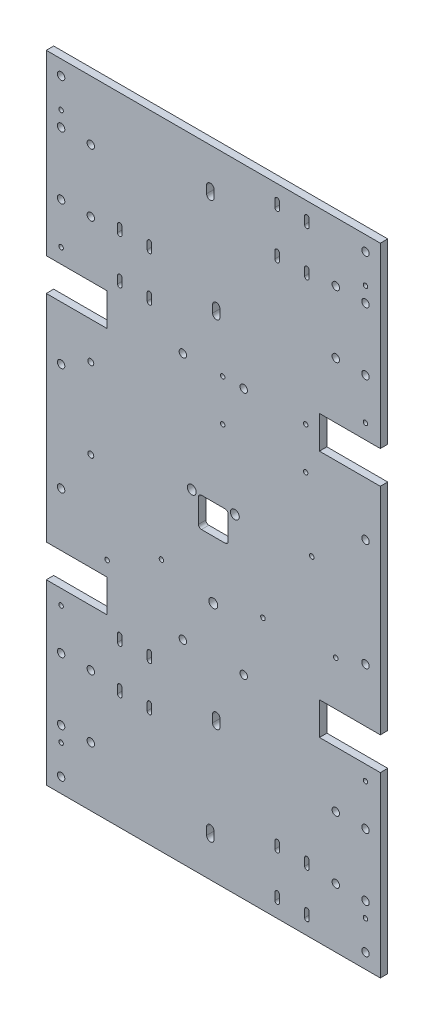
SolidWorks part; units mm, degrees
ref_plane "Front Plane" through (0, 0, 0) normal (0, 0, 1) x (1, 0, 0)
ref_plane "Top Plane" through (0, 0, 0) normal (0, 1, 0) x (1, 0, 0)
ref_plane "Right Plane" through (0, 0, 0) normal (1, 0, 0) x (0, 0, -1)
sketch "Sketch1" plane through (0, 0, 0) normal (0, 0, 1) x (1, 0, 0)
  line L0 (-112.5, 72.5) -> (-112.5, -72.5)
  line L2 (-112.5, 244.5) -> (-112.5, 94.5)
  line L4 (112.5, 244.5) -> (112.5, 94.5)
  line L5 (-112.5, 244.5) -> (112.5, -244.5) construction
  line L6 (-112.5, -244.5) -> (112.5, 244.5) construction
  line L7 (-112.5, 94.5) -> (-71.5, 94.5)
  line L10 (-71.5, 94.5) -> (-71.5, 72.5)
  line L11 (112.5, 94.5) -> (71.5, 94.5)
  line L13 (112.5, 72.5) -> (71.5, 72.5)
  line L14 (71.5, 94.5) -> (71.5, 72.5)
  line L15 (-112.5, -94.5) -> (-71.5, -94.5)
  line L17 (-112.5, -72.5) -> (-71.5, -72.5)
  line L18 (-71.5, -94.5) -> (-71.5, -72.5)
  line L19 (112.5, -72.5) -> (71.5, -72.5)
  line L21 (112.5, -94.5) -> (71.5, -94.5)
  line L22 (71.5, -72.5) -> (71.5, -94.5)
  line L23 (112.5, 72.5) -> (112.5, -72.5)
  line L24 (112.5, -94.5) -> (112.5, -244.5)
  line L25 (-112.5, -94.5) -> (-112.5, -244.5)
  line L28 (-112.5, 72.5) -> (-71.5, 72.5)
  line L30 (-112.5, -244.5) -> (112.5, -244.5) construction
  line L31 (112.5, -244.5) -> (-112.5, -244.5)
  line L32 (112.5, 244.5) -> (-112.5, 244.5)
  point P0 (0, 0)
  dimension "D2" = 225
  dimension "D3" = 41
  dimension "D6" = 22
  dimension "D7" = 22
  dimension "D8" = 41
  dimension "D9" = 41
  dimension "D10" = 22
  dimension "D12" = 145
  dimension "D67" = 150
extrude "Boss-Extrude1" add sketch "Sketch1" along normal blind 5
sketch "Sketch4" plane through (0, 0, 5) normal (0, 0, 1) x (1, 0, 0)
  line L0 (-112.5, 244.5) -> (-112.5, 94.5) construction
  line L1 (-112.5, 94.5) -> (-71.5, 94.5) construction
  circle A0 centre (-102.5, 174.31) radius 2.5
  circle A1 centre (-102.5, 132.31) radius 2.5
  circle A6 centre (-82.5, 174.31) radius 2.5
  circle A7 centre (-82.5, 132.31) radius 2.5
  dimension "D9" = 5
  dimension "D10" = 10
  dimension "D11" = 37.81
  dimension "D12" = 42
  dimension "D13" = 10
  dimension "D2" = 42
  dimension "D3" = 20
  dimension "D4" = 20
  dimension "D5" = 37.81
extrude "Cut-Extrude2" cut sketch "Sketch4" against normal blind 10
mirror "Mirror1" about plane through (0, 0, 0) normal (1, 0, 0) of "Cut-Extrude2"
mirror "Mirror2" about plane through (0, 0, 0) normal (0, 1, 0) of "Mirror1", "Cut-Extrude2"
sketch "Sketch5" plane through (0, 0, 5) normal (0, 0, 1) x (1, 0, 0)
  line L0 (-112.5, 244.5) -> (-112.5, 94.5) construction
  line L1 (-71.5, 72.5) -> (-112.5, 72.5) construction
  line L2 (-112.5, 72.5) -> (-112.5, -72.5) construction
  line L3 (-112.5, -72.5) -> (-71.5, -72.5) construction
  line L4 (-112.5, -94.5) -> (-112.5, -244.5) construction
  line L5 (112.5, -72.5) -> (112.5, 72.5) construction
  line L6 (112.5, 72.5) -> (71.5, 72.5) construction
  line L7 (-71.5, -72.5) -> (-71.5, -94.5) construction
  line L8 (71.5, -94.5) -> (71.5, -72.5) construction
  line L9 (-71.5, -83.5) -> (71.5, -83.5) construction
  line L10 (-71.5, 83.5) -> (71.5, 83.5) construction
  line L11 (-71.5, 94.5) -> (-71.5, 72.5) construction
  line L12 (71.5, 72.5) -> (71.5, 94.5) construction
  line L13 (112.5, 94.5) -> (112.5, 244.5) construction
  line L16 (0, 0) -> (82.5, 0) construction
  line L17 (71.5, -72.5) -> (112.5, -72.5) construction
  line L18 (0, 0) -> (0, -51.9509) construction
  line L28 (62.2018, 55.56) -> (62.2018, 83.5) construction
  line L29 (6.3218, 83.5) -> (6.3218, 55.56) construction
  line L30 (6.3218, 55.56) -> (62.2018, 55.56) construction
  line L31 (6.3218, 83.5) -> (62.2018, 55.56) construction
  line L32 (62.2018, 83.5) -> (6.3218, 83.5) construction
  circle A0 centre (-102.5, 204.31) radius 2.5
  circle A1 centre (-102.5, 174.31) radius 2.5 construction
  circle A2 centre (-102.5, 36.25) radius 2.5
  circle A3 centre (-102.5, -36.25) radius 2.5
  circle A5 centre (-102.5, -204.31) radius 2.5
  circle A6 centre (-102.5, -174.31) radius 2.5 construction
  circle A7 centre (102.5, -204.31) radius 2.5
  circle A8 centre (102.5, 204.31) radius 2.5
  circle A9 centre (102.5, 36.25) radius 2.5
  circle A11 centre (-20.5, -83.5) radius 2.5
  circle A12 centre (20.5, -83.5) radius 2.5
  circle A14 centre (-20.5, 83.5) radius 2.5
  circle A15 centre (20.5, 83.5) radius 2.5
  circle A16 centre (102.5, -174.31) radius 2.5 construction
  circle A17 centre (102.5, 174.31) radius 2.5 construction
  circle A19 centre (102.5, -36.25) radius 2.5
  circle A43 centre (62.2018, 83.5) radius 1.5
  circle A44 centre (62.2018, 55.56) radius 1.5
  circle A45 centre (6.3218, 55.56) radius 1.5
  circle A46 centre (6.3218, 83.5) radius 1.5
  dimension "D1" = 5
  dimension "D2" = 10
  dimension "D3" = 30
  dimension "D4" = 36.25
  dimension "D5" = 36.25
  dimension "D6" = 10
  dimension "D7" = 10
  dimension "D8" = 36.25
  dimension "D9" = 10
  dimension "D10" = 0
  dimension "D14" = 10
  dimension "D15" = 30
  dimension "D17" = 30
  dimension "D18" = 10
  dimension "D20" = 10
  dimension "D21" = 36.25
  dimension "D23" = 51
  dimension "D24" = 51
  dimension "D25" = 10
  dimension "D26" = 5
  dimension "D27" = 5
  dimension "D28" = 30
  dimension "D30" = 5
  dimension "D32" = 51
  dimension "D33" = 5
  dimension "D42" = 3
  dimension "D31" = 51
  dimension "D43" = 55.88
  dimension "D44" = 27.94
  dimension "D45" = 62.4757
extrude "Cut-Extrude3" cut sketch "Sketch5" against normal blind 60
sketch "Sketch6" plane through (0, 0, 5) normal (0, 0, 1) x (1, 0, 0)
  line L2 (-112.5, 72.5) -> (-112.5, -72.5) construction
  line L3 (2.75, 0) -> (-2.75, 0) construction
  line L4 (-112.5, 94.5) -> (-71.5, 94.5) construction
  line L5 (71.5, 94.5) -> (112.5, 94.5) construction
  line L6 (82.5, -42.5) -> (33.45, -43.7) construction
  line L7 (33.45, -43.7) -> (66.3, 8.5) construction
  line L8 (112.5, 94.5) -> (112.5, 244.5) construction
  line L9 (66.3, 8.5) -> (82.5, -42.5) construction
  line L10 (112.5, -72.5) -> (112.5, 72.5) construction
  line L11 (71.5, -72.5) -> (112.5, -72.5) construction
  line L12 (-71.5, 72.5) -> (-112.5, 72.5) construction
  circle A15 centre (33.45, -43.7) radius 1.55
  circle A16 centre (82.5, -42.5) radius 1.55
  circle A18 centre (66.3, 8.5) radius 1.55
  circle A21 centre (102.5, -104.5) radius 1.5
  circle A22 centre (-102.5, -104.5) radius 1.5
  circle A23 centre (102.5, 184.5) radius 1.5
  circle A24 centre (-102.5, 184.5) radius 1.5
  circle A25 centre (-102.5, 104.5) radius 1.5
  circle A26 centre (102.5, 104.5) radius 1.5
  circle A27 centre (-102.5, -184.5) radius 1.5
  circle A28 centre (102.5, -184.5) radius 1.5
  circle A29 centre (-82.5, 47.5) radius 2
  circle A30 centre (-82.5, -6.5) radius 2
  dimension "D4" = 4
  dimension "D5" = 4
  dimension "D6" = 54
  dimension "D7" = 56.416
  dimension "D8" = 49.0647
  dimension "D9" = 61.6763
  dimension "D10" = 30
  dimension "D11" = 46.2
  dimension "D12" = 30
  dimension "D13" = 30
  dimension "D14" = 25
  dimension "D15" = 30
  dimension "D23" = 80
  dimension "D25" = 10
  dimension "D28" = 3.1
  dimension "D29" = 3
  dimension "D30" = 0
  dimension "D31" = 0
  dimension "D32" = 10
  dimension "D33" = 80
  dimension "D34" = 205
  dimension "D35" = 10
extrude "Cut-Extrude4" cut sketch "Sketch6" against normal blind 10
sketch "Sketch7" plane through (0, 0, 0) normal (0, 0, -1) x (1, 0, 0)
  line L0 (43, 204.62) -> (43, 199.62) construction
  line L1 (43, 169.62) -> (43, 174.62) construction
  line L2 (44.5, 204.62) -> (44.5, 199.62)
  line L3 (41.5, 204.62) -> (41.5, 199.62)
  line L4 (43, 202.12) -> (43, 172.12) construction
  line L5 (63, 199.62) -> (63, 204.62) construction
  line L6 (61.5, 199.62) -> (61.5, 204.62)
  line L7 (64.5, 199.62) -> (64.5, 204.62)
  line L8 (41.5, 169.62) -> (41.5, 174.62)
  line L11 (63, 169.62) -> (63, 174.62) construction
  line L12 (61.5, 169.62) -> (61.5, 174.62)
  line L13 (64.5, 169.62) -> (64.5, 174.62)
  line L14 (44.5, 169.62) -> (44.5, 174.62)
  line L17 (-43, 132) -> (-43, 137) construction
  line L18 (-44.5, 132) -> (-44.5, 137)
  line L19 (-41.5, 132) -> (-41.5, 137)
  line L20 (-63, 132) -> (-63, 137) construction
  line L21 (-64.5, 132) -> (-64.5, 137)
  line L22 (-61.5, 132) -> (-61.5, 137)
  line L23 (-43, 102) -> (-43, 107) construction
  line L24 (-44.5, 102) -> (-44.5, 107)
  line L25 (-41.5, 102) -> (-41.5, 107)
  line L26 (-63, 102) -> (-63, 107) construction
  line L27 (-64.5, 102) -> (-64.5, 107)
  line L28 (-61.5, 102) -> (-61.5, 107)
  line L29 (-43, -102) -> (-43, -107) construction
  line L30 (-41.5, -102) -> (-41.5, -107)
  line L31 (-44.5, -102) -> (-44.5, -107)
  line L32 (-63, -102) -> (-63, -107) construction
  line L33 (-61.5, -102) -> (-61.5, -107)
  line L34 (-64.5, -102) -> (-64.5, -107)
  line L35 (-43, -137) -> (-43, -132) construction
  line L36 (-44.5, -137) -> (-44.5, -132)
  line L37 (-41.5, -137) -> (-41.5, -132)
  line L38 (-63, -137) -> (-63, -132) construction
  line L39 (-64.5, -137) -> (-64.5, -132)
  line L40 (-61.5, -137) -> (-61.5, -132)
  line L41 (63, -174.62) -> (63, -169.62) construction
  line L42 (61.5, -174.62) -> (61.5, -169.62)
  line L43 (64.5, -174.62) -> (64.5, -169.62)
  line L44 (43, -174.62) -> (43, -169.62) construction
  line L45 (41.5, -174.62) -> (41.5, -169.62)
  line L46 (44.5, -174.62) -> (44.5, -169.62)
  line L47 (63, -204.62) -> (63, -199.62) construction
  line L48 (61.5, -204.62) -> (61.5, -199.62)
  line L49 (64.5, -204.62) -> (64.5, -199.62)
  line L50 (43, -204.62) -> (43, -199.62) construction
  line L51 (41.5, -204.62) -> (41.5, -199.62)
  line L52 (44.5, -204.62) -> (44.5, -199.62)
  line L54 (43, 187.12) -> (-2, 187.12) construction
  line L55 (-43, 134.5) -> (-43, 104.5) construction
  line L56 (-43, 104.5) -> (-43, 119.5) construction
  line L57 (-43, 119.5) -> (2, 119.5) construction
  line L58 (-43, -108.5) -> (-43, -130.5) construction
  line L59 (-43, -119.5) -> (2, -119.5) construction
  line L60 (43, -202.12) -> (43, -172.12) construction
  line L61 (43, -187.12) -> (-2, -187.12) construction
  line L62 (2, -117) -> (2, -122) construction
  line L63 (4.5, -117) -> (4.5, -122)
  line L64 (-0.5, -117) -> (-0.5, -122)
  line L65 (-2, -184.62) -> (-2, -189.62) construction
  line L66 (0.5, -184.62) -> (0.5, -189.62)
  line L67 (-4.5, -184.62) -> (-4.5, -189.62)
  line L68 (2, 122) -> (2, 117) construction
  line L69 (4.5, 122) -> (4.5, 117)
  line L70 (-0.5, 122) -> (-0.5, 117)
  line L71 (-2, 189.62) -> (-2, 184.62) construction
  line L72 (0.5, 189.62) -> (0.5, 184.62)
  line L73 (-4.5, 189.62) -> (-4.5, 184.62)
  arc A2 (61.5, 199.62) -> (64.5, 199.62) centre (63, 199.62) ccw
  arc A3 (44.5, 204.62) -> (41.5, 204.62) centre (43, 204.62) ccw
  arc A4 (64.5, 204.62) -> (61.5, 204.62) centre (63, 204.62) ccw
  arc A9 (61.5, 169.62) -> (64.5, 169.62) centre (63, 169.62) ccw
  arc A10 (64.5, 174.62) -> (61.5, 174.62) centre (63, 174.62) ccw
  arc A15 (-44.5, 132) -> (-41.5, 132) centre (-43, 132) ccw
  arc A16 (-41.5, 137) -> (-44.5, 137) centre (-43, 137) ccw
  arc A18 (-64.5, 132) -> (-61.5, 132) centre (-63, 132) ccw
  arc A19 (-61.5, 137) -> (-64.5, 137) centre (-63, 137) ccw
  arc A21 (-44.5, 102) -> (-41.5, 102) centre (-43, 102) ccw
  arc A22 (-41.5, 107) -> (-44.5, 107) centre (-43, 107) ccw
  arc A24 (-64.5, 102) -> (-61.5, 102) centre (-63, 102) ccw
  arc A25 (-61.5, 107) -> (-64.5, 107) centre (-63, 107) ccw
  arc A27 (-41.5, -102) -> (-44.5, -102) centre (-43, -102) ccw
  arc A28 (-44.5, -107) -> (-41.5, -107) centre (-43, -107) ccw
  arc A30 (-61.5, -102) -> (-64.5, -102) centre (-63, -102) ccw
  arc A31 (-64.5, -107) -> (-61.5, -107) centre (-63, -107) ccw
  arc A33 (-44.5, -137) -> (-41.5, -137) centre (-43, -137) ccw
  arc A34 (-41.5, -132) -> (-44.5, -132) centre (-43, -132) ccw
  arc A36 (-64.5, -137) -> (-61.5, -137) centre (-63, -137) ccw
  arc A37 (-61.5, -132) -> (-64.5, -132) centre (-63, -132) ccw
  arc A39 (61.5, -174.62) -> (64.5, -174.62) centre (63, -174.62) ccw
  arc A40 (64.5, -169.62) -> (61.5, -169.62) centre (63, -169.62) ccw
  arc A42 (41.5, -174.62) -> (44.5, -174.62) centre (43, -174.62) ccw
  arc A43 (44.5, -169.62) -> (41.5, -169.62) centre (43, -169.62) ccw
  arc A46 (61.5, -204.62) -> (64.5, -204.62) centre (63, -204.62) ccw
  arc A48 (64.5, -199.62) -> (61.5, -199.62) centre (63, -199.62) ccw
  arc A49 (41.5, -204.62) -> (44.5, -204.62) centre (43, -204.62) ccw
  arc A50 (44.5, -199.62) -> (41.5, -199.62) centre (43, -199.62) ccw
  arc A51 (41.5, 199.62) -> (44.5, 199.62) centre (43, 199.62) ccw
  arc A52 (41.5, 169.62) -> (44.5, 169.62) centre (43, 169.62) ccw
  arc A53 (44.5, 174.62) -> (41.5, 174.62) centre (43, 174.62) ccw
  circle A55 centre (-82.5, -132.31) radius 2.5 construction
  circle A56 centre (82.5, 174.31) radius 2.5 construction
  circle A57 centre (-82.5, 132.31) radius 2.5 construction
  circle A58 centre (82.5, -174.31) radius 2.5 construction
  arc A62 (4.5, -117) -> (-0.5, -117) centre (2, -117) ccw
  arc A63 (-0.5, -122) -> (4.5, -122) centre (2, -122) ccw
  arc A64 (0.5, -184.62) -> (-4.5, -184.62) centre (-2, -184.62) ccw
  arc A65 (-4.5, -189.62) -> (0.5, -189.62) centre (-2, -189.62) ccw
  arc A66 (4.5, 122) -> (-0.5, 122) centre (2, 122) ccw
  arc A67 (-0.5, 117) -> (4.5, 117) centre (2, 117) ccw
  arc A68 (0.5, 189.62) -> (-4.5, 189.62) centre (-2, 189.62) ccw
  arc A69 (-4.5, 184.62) -> (0.5, 184.62) centre (-2, 184.62) ccw
  circle A71 centre (-82.5, -132.31) radius 2.5 construction
  circle A72 centre (82.5, -174.31) radius 2.5 construction
  circle A73 centre (82.5, 174.31) radius 2.5 construction
  circle A74 centre (-82.5, 132.31) radius 2.5 construction
  point P14 (43, 202.12)
  point P23 (43, 172.12)
  point P31 (63, 202.12)
  point P52 (2, -119.5)
  point P56 (63, 172.12)
  point P65 (-2, -187.12)
  point P71 (-43, 134.5)
  point P78 (-63, 134.5)
  point P85 (-43, 104.5)
  point P92 (-63, 104.5)
  point P99 (-43, -104.5)
  point P106 (-63, -104.5)
  point P113 (-43, -134.5)
  point P120 (-63, -134.5)
  point P127 (63, -172.12)
  point P134 (43, -172.12)
  point P141 (63, -202.12)
  point P148 (43, -202.12)
  point P155 (2, 119.5)
  point P161 (-2, 187.12)
  dimension "D18" = 2.19
  dimension "D19" = 20
  dimension "D20" = 30
  dimension "D21" = 20
  dimension "D22" = 30
  dimension "D1" = 20
  dimension "D4" = 30
  dimension "D5" = 1.5
  dimension "D6" = 2.19
  dimension "D7" = 30
  dimension "D8" = 20
  dimension "D9" = 30
  dimension "D10" = 36.0555
  dimension "D11" = 20
  dimension "D12" = 30
  dimension "D13" = 20
  dimension "D14" = 30
  dimension "D15" = 36.0555
  dimension "D16" = 2.19
  dimension "D17" = 5
  dimension "D23" = 36.0555
  dimension "D24" = 2.19
  dimension "D25" = 30
  dimension "D26" = 19.5
  dimension "D27" = 0
  dimension "D28" = 30
  dimension "D29" = 20
  dimension "D30" = 19.5
  dimension "D31" = 1.5
  dimension "D32" = 20
  dimension "D33" = 5
  dimension "D34" = 19.5
  dimension "D35" = 5
  dimension "D36" = 1.5
  dimension "D37" = 0
  dimension "D38" = 19.5
  dimension "D39" = 5
  dimension "D40" = 20
  dimension "D42" = 5
  dimension "D45" = 5
  dimension "D47" = 45
  dimension "D49" = 30
  dimension "D51" = 2.5
  dimension "D54" = 2.5
  dimension "D56" = 2.5
  dimension "D59" = 2.5
  dimension "D41" = 20
  dimension "D43" = 45
  dimension "D44" = 45
  dimension "D46" = 22
  dimension "D48" = 45
  dimension "D50" = 5
  dimension "D52" = 15
  dimension "D53" = 5
  dimension "D55" = 15
  dimension "D57" = 30
  dimension "D58" = 15
extrude "Cut-Extrude5" cut sketch "Sketch7" against normal blind 10
sketch "Sketch8" plane through (0, 0, 5) normal (0, 0, 1) x (1, 0, 0)
  line L1 (-125.813, -254.9936) -> (125.1722, -254.9936)
  line L2 (-125.813, -254.9936) -> (-125.813, -214.31)
  line L3 (-125.813, -214.31) -> (125.1722, -214.31)
  line L4 (125.1722, -254.9936) -> (125.1722, -214.31)
  line L5 (-131.4959, 258.2543) -> (138.2176, 258.2543)
  line L6 (-131.4959, 258.2543) -> (-131.4959, 214.31)
  line L7 (-131.4959, 214.31) -> (138.2176, 214.31)
  line L8 (138.2176, 258.2543) -> (138.2176, 214.31)
  circle A0 centre (-102.5, -204.31) radius 2.5 construction
  circle A1 centre (-102.5, 204.31) radius 2.5 construction
  dimension "D1" = 10
  dimension "D2" = 10
extrude "Cut-Extrude6" cut sketch "Sketch8" against normal blind 10
sketch "Sketch10" plane through (0, 0, 0) normal (0, 0, -1) x (-1, 0, 0)
  line L0 (0, -51.943) -> (-14.5, 7.057) construction
  line L1 (-14.5, 7.057) -> (14.5, 7.057) construction
  line L2 (14.5, 7.057) -> (0, -51.943) construction
  line L3 (0, -51.943) -> (0, -214.31) construction
  line L5 (-8, 7.057) -> (8, 7.057)
  line L6 (-112.5, -214.31) -> (112.5, -214.31) construction
  line L7 (-10, 5.057) -> (-10, -10.943)
  line L8 (-8, -12.943) -> (8, -12.943)
  line L9 (10, 5.057) -> (10, -10.943)
  line L10 (-10, 7.057) -> (10, -12.943) construction
  line L11 (-10, -12.943) -> (10, 7.057) construction
  circle A0 centre (0, -51.943) radius 3
  circle A1 centre (-14.5, 7.057) radius 3
  circle A2 centre (14.5, 7.057) radius 3
  arc A3 (-8, 7.057) -> (-10, 5.057) centre (-8, 5.057) ccw
  arc A4 (8, 7.057) -> (10, 5.057) centre (8, 5.057) cw
  arc A5 (8, -12.943) -> (10, -10.943) centre (8, -10.943) ccw
  arc A6 (-10, -10.943) -> (-8, -12.943) centre (-8, -10.943) ccw
  point P7 (0, -2.943)
  point P13 (0, -214.31)
  dimension "D5" = 6
  dimension "D6" = 6
  dimension "D7" = 6
  dimension "D8" = 20
  dimension "D2" = 14.5
  dimension "D12" = 2
  dimension "D1" = 59
  dimension "D3" = 29
  dimension "D4" = 162.367
  dimension "D9" = 20
  dimension "D10" = 4.5
  dimension "D11" = 0
extrude "Cut-Extrude7" cut sketch "Sketch10" against normal blind 10
sketch "Sketch11" plane through (0, 0, 0) normal (0, 0, -1) x (-1, 0, 0)
  line L1 (112.5, -72.5) -> (132.5, -72.5)
  line L2 (112.5, -72.5) -> (112.5, 72.5)
  line L3 (112.5, 72.5) -> (132.5, 72.5)
  line L4 (132.5, -72.5) -> (132.5, 72.5)
  line L5 (-112.5, -72.5) -> (-132.5, -72.5)
  line L6 (-112.5, -72.5) -> (-112.5, 72.5)
  line L7 (-112.5, 72.5) -> (-132.5, 72.5)
  line L8 (-132.5, -72.5) -> (-132.5, 72.5)
  dimension "D1" = 20
  dimension "D2" = 20
extrude "Boss-Extrude2" [suppressed] add sketch "Sketch11" against normal up to surface (5 mm away)
sketch "Sketch12" plane through (0, 0, 0) normal (0, 0, -1) x (-1, 0, 0)
  line L0 (71.5, -62.5) -> (34.924, -62.5) construction
  line L1 (34.924, -62.5) -> (34.924, -43.958) construction
  line L2 (34.924, -43.958) -> (71.5, -43.958) construction
  line L3 (71.5, -43.958) -> (71.5, -62.5) construction
  line L4 (71.5, -72.5) -> (71.5, -94.5) construction
  line L5 (112.5, -72.5) -> (71.5, -72.5) construction
  circle A0 centre (71.5, -62.5) radius 1.5
  circle A1 centre (34.924, -43.958) radius 1.5
  dimension "D3" = 3
  dimension "D4" = 3
  dimension "D5" = 0
  dimension "D1" = 36.576
  dimension "D2" = 18.542
  dimension "D6" = 10
extrude "Cut-Extrude8" cut sketch "Sketch12" against normal blind 10
